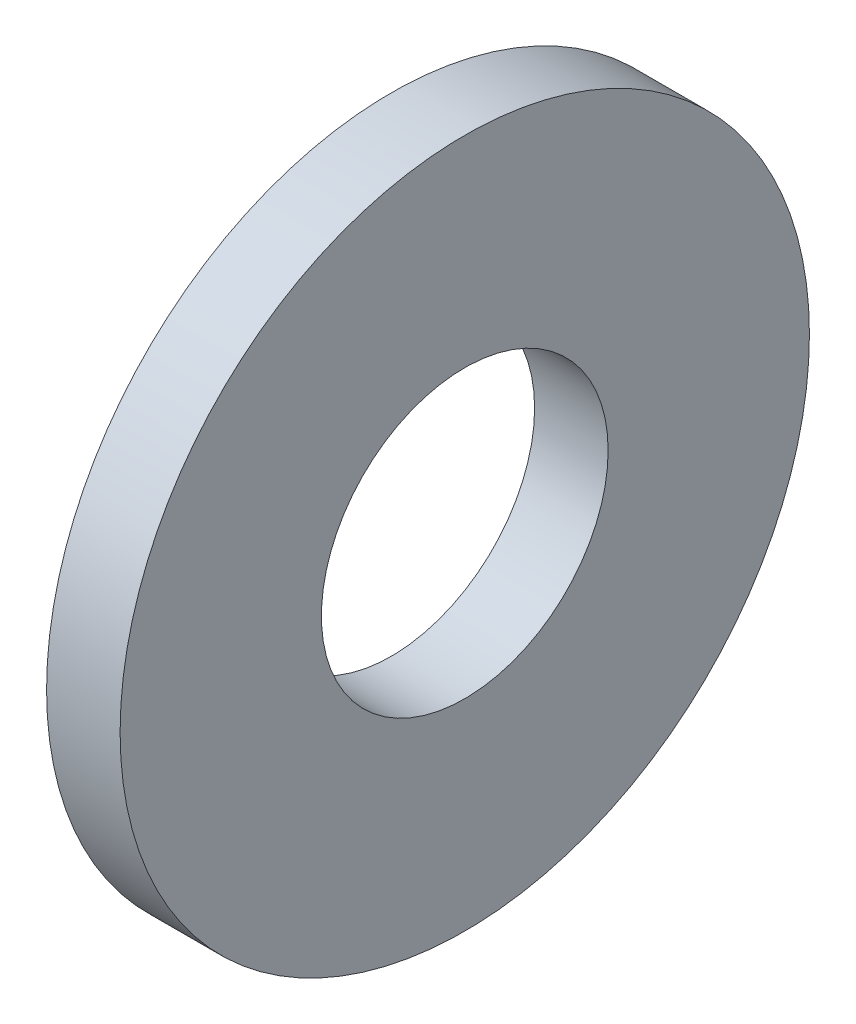
SolidWorks part; units mm, degrees
material "Plain Carbon Steel"
ref_plane "Front Plane" through (0, 0, 0) normal (0, 0, 1) x (1, 0, 0)
ref_plane "Top Plane" through (0, 0, 0) normal (0, 1, 0) x (1, 0, 0)
ref_plane "Right Plane" through (0, 0, 0) normal (1, 0, 0) x (0, 0, -1)
sketch "Sketch1" plane through (0, 0, 0) normal (1, 0, 0) x (0, 0, -1)
  circle A0 centre (0, 0) radius 9.525
  circle A1 centre (0, 0) radius 3.9624
  dimension "OD" = 19.05
  dimension "ID" = 7.9248
extrude "Boss-Extrude1" add sketch "Sketch1" along normal blind 2.032
